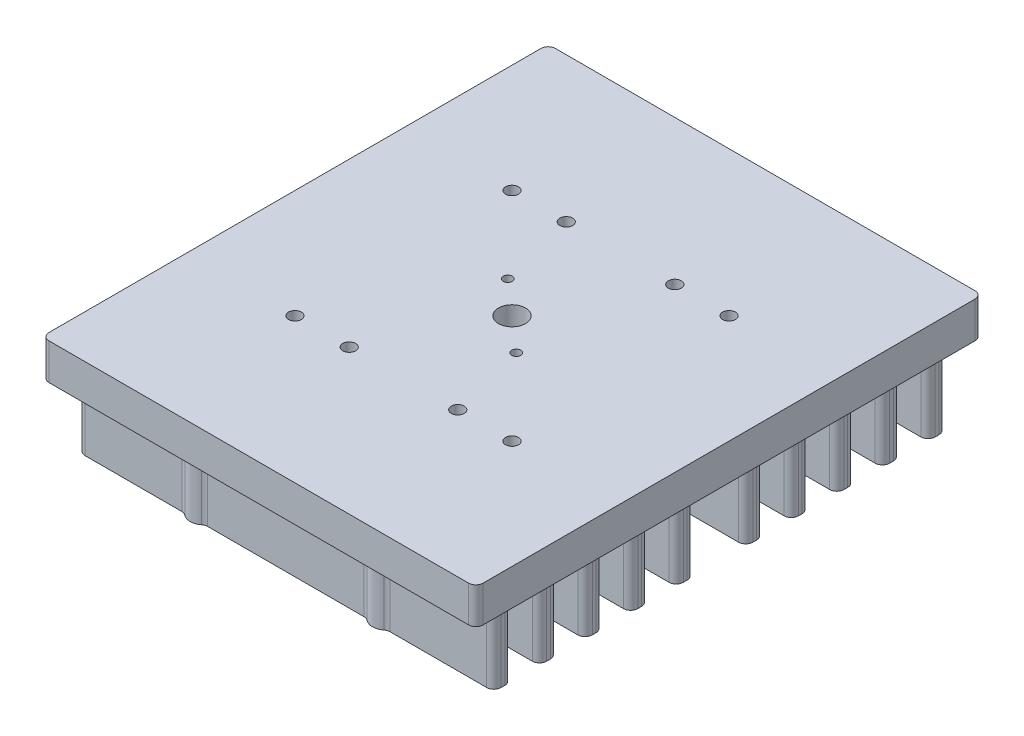
SolidWorks part; units mm, degrees
material "6061-T6 (SS)"
ref_plane "Front Plane" through (0, 0, 0) normal (0, 0, 1) x (1, 0, 0)
ref_plane "Top Plane" through (0, 0, 0) normal (0, 1, 0) x (1, 0, 0)
ref_plane "Right Plane" through (0, 0, 0) normal (1, 0, 0) x (0, 0, -1)
sketch "Sketch1" plane through (0, 0, 0) normal (0, 1, 0) x (1, 0, 0)
  line L1 (25.4, -25.4) -> (-25.4, -25.4) construction
  line L2 (25.4, -25.4) -> (25.4, 25.4) construction
  line L3 (25.4, 25.4) -> (-25.4, 25.4) construction
  line L4 (-25.4, -25.4) -> (-25.4, 25.4) construction
  line L5 (25.4, -25.4) -> (-25.4, 25.4) construction
  line L6 (25.4, 25.4) -> (-25.4, -25.4) construction
  line L7 (-38.1, 44.45) -> (38.1, 44.45)
  line L8 (-38.1, 44.45) -> (-38.1, -44.45)
  line L9 (-38.1, -44.45) -> (38.1, -44.45)
  line L10 (38.1, 44.45) -> (38.1, -44.45)
  line L11 (-38.1, 44.45) -> (38.1, -44.45) construction
  line L12 (-38.1, -44.45) -> (38.1, 44.45) construction
  point P0 (0, 0)
  point P6 (0, 0)
  dimension "D1" = 50.8
  dimension "D2" = 50.8
  dimension "D3" = 76.2
  dimension "D4" = 88.9
extrude "Boss-Extrude1" add sketch "Sketch1" along normal blind 6.35
hole_wizard "#4-40 Tapped Hole1" positions "Sketch2" profile "Sketch3" tap size "#4-40" standard "ANSI Inch" end condition through all
sketch "Sketch2" plane through (0, 6.35, 0) normal (0, 1, 0) x (1, 0, 0)
  line L1 (-19.05, 19.05) -> (19.05, 19.05)
  line L2 (-19.05, 19.05) -> (-19.05, -19.05)
  line L3 (-19.05, -19.05) -> (19.05, -19.05)
  line L4 (19.05, 19.05) -> (19.05, -19.05)
  line L5 (-19.05, 19.05) -> (19.05, -19.05) construction
  line L6 (-19.05, -19.05) -> (19.05, 19.05) construction
  point P2 (19.05, -19.05)
  point P51 (-19.05, 19.05)
  point P52 (-19.05, -19.05)
  point P53 (19.05, 19.05)
  dimension "D1" = 38.1
  dimension "D2" = 38.1
sketch "Sketch3" plane through (19.05, 6.35, 19.05) normal (1, 0, 0) x (0, 0, 1)
  line L0 (0, 0) -> (0, 6.35)
  line L1 (0, 6.35) -> (1.1303, 6.35)
  line L2 (1.1303, 6.35) -> (1.1303, 0)
  line L5 (1.1303, 0) -> (0, 0)
  line L11 (0, -6.35) -> (0, 107.95) construction
  dimension "Thru Tap Drill Dia." = 2.2606
  dimension "Thru Tap Drill Depth" = 6.35
cosmetic thread "Hole Thread1" parameters "D2"=2.8448
cosmetic thread "Hole Thread2" parameters "D2"=2.8448
cosmetic thread "Hole Thread3" parameters "D2"=2.8448
cosmetic thread "Hole Thread4" parameters "D2"=2.8448
hole_wizard "M2x0.4 Tapped Hole1" positions "Sketch4" profile "Sketch5" tap size "M2x0.4" standard "ANSI Metric" end condition through all
sketch "Sketch4" plane through (0, 6.35, 0) normal (0, 1, 0) x (1, 0, 0)
  line L0 (-6, 5.25) -> (6, -5.25) construction
  point P0 (-6, 5.25)
  point P2 (6, -5.25)
  dimension "D1" = 12
  dimension "D2" = 10.5
sketch "Sketch5" plane through (-6, 6.35, -5.25) normal (1, 0, 0) x (0, 0, 1)
  line L0 (0, 0) -> (0, 6.35)
  line L1 (0, 6.35) -> (0.8, 6.35)
  line L2 (0.8, 6.35) -> (0.8, 0)
  line L5 (0.8, 0) -> (0, 0)
  line L11 (0, -6.35) -> (0, 107.95) construction
  dimension "Thru Tap Drill Dia." = 1.6
  dimension "Thru Tap Drill Depth" = 6.35
cosmetic thread "Hole Thread5" parameters "D2"=2
cosmetic thread "Hole Thread6" parameters "D2"=2
sketch "Sketch6" plane through (0, 0, 0) normal (0, -1, 0) x (1, 0, 0)
  line L0 (0, 22.1) -> (0, 0) construction
  line L1 (-16, 38.1) -> (16, 38.1) construction
  line L2 (-16, 38.1) -> (-16, 6.1) construction
  line L3 (-16, 6.1) -> (16, 6.1) construction
  line L4 (16, 38.1) -> (16, 6.1) construction
  line L5 (-16, 38.1) -> (16, 6.1) construction
  line L6 (-16, 6.1) -> (16, 38.1) construction
  line L8 (-38.1, 44.45) -> (38.1, 44.45) construction
  line L9 (-1000, 0) -> (49000, 0) construction
  line L10 (-16, -6.1) -> (16, -38.1) construction
  line L11 (-16, -38.1) -> (16, -6.1) construction
  line L12 (16, -38.1) -> (16, -6.1) construction
  line L13 (-16, -6.1) -> (16, -6.1) construction
  line L14 (-16, -38.1) -> (-16, -6.1) construction
  line L15 (-16, -38.1) -> (16, -38.1) construction
  circle A0 centre (-16, 38.1) radius 2.3812
  circle A1 centre (16, 38.1) radius 2.3813
  arc A2 (18.3813, 6.1) -> (13.6188, 6.1) centre (16, 6.1) ccw construction
  arc A3 (-13.6187, 6.1) -> (-18.3813, 6.1) centre (-16, 6.1) ccw construction
  circle A4 centre (-16, 6.1) radius 2.3813
  circle A5 centre (16, 6.1) radius 2.3812
  arc A6 (-13.6187, -6.1) -> (-18.3813, -6.1) centre (-16, -6.1) cw construction
  arc A7 (18.3813, -6.1) -> (13.6188, -6.1) centre (16, -6.1) cw construction
  circle A8 centre (16, -6.1) radius 2.3812
  circle A9 centre (-16, -6.1) radius 2.3813
  circle A10 centre (16, -38.1) radius 2.3813
  circle A11 centre (-16, -38.1) radius 2.3812
  point P0 (0, 0)
  dimension "D3" = 4.7625
  dimension "D1" = 32
  dimension "D2" = 32
  dimension "D4" = 6.35
extrude "Boss-Extrude2" add sketch "Sketch6" along normal blind 12.7
sketch "Sketch9" plane through (0, 0, 0) normal (0, -1, 0) x (1, 0, 0)
  line L0 (-36.5125, 38.1) -> (-16, 38.1) construction
  line L1 (-36.5125, 39.6875) -> (36.5125, 39.6875)
  line L2 (-36.5125, 39.6875) -> (-36.5125, 36.5125)
  line L3 (-36.5125, 36.5125) -> (36.5125, 36.5125)
  line L4 (36.5125, 39.6875) -> (36.5125, 36.5125)
  line L5 (-38.1, -44.45) -> (-38.1, 44.45) construction
  line L6 (-36.5125, 31.6875) -> (36.5125, 31.6875)
  line L7 (-36.5125, 31.6875) -> (-36.5125, 28.5125)
  line L8 (-36.5125, 28.5125) -> (36.5125, 28.5125)
  line L9 (36.5125, 31.6875) -> (36.5125, 28.5125)
  line L10 (-36.5125, 23.6875) -> (36.5125, 23.6875)
  line L11 (-36.5125, 23.6875) -> (-36.5125, 20.5125)
  line L12 (-36.5125, 20.5125) -> (36.5125, 20.5125)
  line L13 (36.5125, 23.6875) -> (36.5125, 20.5125)
  line L14 (-36.5125, 15.6875) -> (36.5125, 15.6875)
  line L15 (-36.5125, 15.6875) -> (-36.5125, 12.5125)
  line L16 (-36.5125, 12.5125) -> (36.5125, 12.5125)
  line L17 (36.5125, 15.6875) -> (36.5125, 12.5125)
  line L18 (38.1, 44.45) -> (38.1, -44.45) construction
  line L19 (-38.1, 44.45) -> (38.1, 44.45) construction
  line L20 (-36.5125, 36.5125) -> (-36.5125, 31.6875) construction
  line L21 (-36.5125, 28.5125) -> (-36.5125, 23.6875) construction
  line L22 (-36.5125, 20.5125) -> (-36.5125, 15.6875) construction
  line L23 (-36.5125, 12.5125) -> (-36.5125, 7.6875) construction
  line L24 (-36.5125, -6.1) -> (-16, -6.1) construction
  line L25 (-36.5125, 7.6875) -> (36.5125, 7.6875)
  line L26 (-36.5125, 7.6875) -> (-36.5125, 4.5125)
  line L27 (-36.5125, -12.5125) -> (-36.5125, -7.6875) construction
  line L28 (-36.5125, 6.1) -> (-16, 6.1) construction
  line L29 (-1000, 0) -> (49000, 0) construction
  line L30 (-36.5125, -20.5125) -> (-36.5125, -15.6875) construction
  line L31 (-36.5125, -28.5125) -> (-36.5125, -23.6875) construction
  line L32 (-36.5125, -36.5125) -> (-36.5125, -31.6875) construction
  line L33 (-36.5125, -38.1) -> (-16, -38.1) construction
  line L34 (-36.5125, 4.5125) -> (36.5125, 4.5125)
  line L35 (36.5125, 7.6875) -> (36.5125, 4.5125)
  line L36 (36.5125, -7.6875) -> (36.5125, -4.5125)
  line L37 (-36.5125, -4.5125) -> (36.5125, -4.5125)
  line L38 (-36.5125, -7.6875) -> (-36.5125, -4.5125)
  line L39 (-36.5125, -7.6875) -> (36.5125, -7.6875)
  line L40 (36.5125, -15.6875) -> (36.5125, -12.5125)
  line L41 (-36.5125, -12.5125) -> (36.5125, -12.5125)
  line L42 (-36.5125, -15.6875) -> (-36.5125, -12.5125)
  line L43 (-36.5125, -15.6875) -> (36.5125, -15.6875)
  line L44 (36.5125, -23.6875) -> (36.5125, -20.5125)
  line L45 (-36.5125, -20.5125) -> (36.5125, -20.5125)
  line L46 (-36.5125, -23.6875) -> (-36.5125, -20.5125)
  line L47 (-36.5125, -23.6875) -> (36.5125, -23.6875)
  line L48 (36.5125, -31.6875) -> (36.5125, -28.5125)
  line L49 (-36.5125, -28.5125) -> (36.5125, -28.5125)
  line L50 (-36.5125, -31.6875) -> (-36.5125, -28.5125)
  line L51 (-36.5125, -31.6875) -> (36.5125, -31.6875)
  line L52 (36.5125, -39.6875) -> (36.5125, -36.5125)
  line L53 (-36.5125, -36.5125) -> (36.5125, -36.5125)
  line L54 (-36.5125, -39.6875) -> (-36.5125, -36.5125)
  line L55 (-36.5125, -39.6875) -> (36.5125, -39.6875)
  dimension "D1" = 1.5875
  dimension "D2" = 1.5875
  dimension "D3" = 4.7625
  dimension "D4" = 4.825
extrude "Boss-Extrude3" add sketch "Sketch9" along normal blind 12.7
hole_wizard "#6-32 Tapped Hole1" positions "Sketch7" profile "Sketch8" tap size "#6-32" standard "ANSI Inch"
sketch "Sketch7" plane through (0, -12.7, 0) normal (0, -1, 0) x (-1, 0, 0)
  point P0 (16, -38.1)
  point P3 (-16, -38.1)
  point P32 (-16, 38.1)
  point P35 (16, 38.1)
  point P38 (-16, 6.1)
  point P41 (16, 6.1)
  point P43 (16, -6.1)
  point P46 (-16, -6.1)
cosmetic thread "Hole Thread7" [suppressed] parameters "D1"=7.0104, "D2"=3.5052
cosmetic thread "Hole Thread8" [suppressed] parameters "D1"=7.0104, "D2"=3.5052
cosmetic thread "Hole Thread9" [suppressed] parameters "D1"=7.0104, "D2"=3.5052
cosmetic thread "Hole Thread10" [suppressed] parameters "D1"=7.0104, "D2"=3.5052
sketch "Sketch8" plane through (-16, -12.7, 38.1) normal (1, 0, 0) x (0, 0, -1)
  line L0 (0, 0) -> (0, 10.2107)
  line L1 (0, 10.2107) -> (1.3525, 9.398)
  line L2 (1.3525, 9.398) -> (1.3525, 0)
  line L5 (1.3525, 0) -> (0, 0)
  line L10 (0, 10.2107) -> (-1.3525, 9.398) construction
  line L11 (0, -6.35) -> (0, 107.95) construction
  dimension "Tap Drill Dia." = 2.7051
  dimension "Tap Drill Depth" = 9.398
  dimension "Drill Angle" = 118
cosmetic thread "Hole Thread11" parameters "D1"=7.0104, "D2"=3.5052
cosmetic thread "Hole Thread12" parameters "D1"=7.0104, "D2"=3.5052
cosmetic thread "Hole Thread13" parameters "D1"=7.0104, "D2"=3.5052
cosmetic thread "Hole Thread14" parameters "D1"=7.0104, "D2"=3.5052
fillet "Fillet1" radius 1.27 76 edges at (-17.7749, -6.35, 39.6875) (-14.2251, -6.35, 39.6875) (14.2251, -6.35, 39.6875) (17.7749, -6.35, 39.6875) (-14.2251, -6.35, 36.5125) (-17.7749, -6.35, 36.5125) (17.7749, -6.35, 36.5125) (14.2251, -6.35, 36.5125) (36.5125, -6.35, 39.6875) (36.5125, -6.35, 36.5125) (36.5125, -6.35, 31.6875) (36.5125, -6.35, 28.5125) (36.5125, -6.35, 23.6875) (36.5125, -6.35, 20.5125) (36.5125, -6.35, 15.6875) (36.5125, -6.35, 12.5125) (-36.5125, -6.35, 39.6875) (-36.5125, -6.35, 36.5125) (-36.5125, -6.35, 31.6875) (-36.5125, -6.35, 28.5125) (-36.5125, -6.35, 23.6875) (-36.5125, -6.35, 20.5125) (-36.5125, -6.35, 15.6875) (-36.5125, -6.35, 12.5125) (-36.5125, -6.35, -39.6875) (-36.5125, -6.35, -36.5125) (-36.5125, -6.35, -31.6875) (-36.5125, -6.35, -28.5125) (-36.5125, -6.35, -23.6875) (-36.5125, -6.35, -20.5125) (-36.5125, -6.35, -15.6875) (-36.5125, -6.35, -12.5125) (-36.5125, -6.35, -7.6875) (-36.5125, -6.35, -4.5125) (-36.5125, -6.35, 4.5125) (-36.5125, -6.35, 7.6875) (14.2251, -6.35, -36.5125) (17.7749, -6.35, -36.5125) (-17.7749, -6.35, -36.5125) (-14.2251, -6.35, -36.5125) (17.7749, -6.35, -39.6875) (14.2251, -6.35, -39.6875) (-14.2251, -6.35, -39.6875) (-17.7749, -6.35, -39.6875) (17.7749, -6.35, -7.6875) (14.2251, -6.35, -7.6875) (-14.2251, -6.35, -7.6875) (-17.7749, -6.35, -7.6875) (14.2251, -6.35, -4.5125) (17.7749, -6.35, -4.5125) (-17.7749, -6.35, -4.5125) (-14.2251, -6.35, -4.5125) (17.7749, -6.35, 4.5125) (14.2251, -6.35, 4.5125) (-14.2251, -6.35, 4.5125) (-17.7749, -6.35, 4.5125) (-17.7749, -6.35, 7.6875) (-14.2251, -6.35, 7.6875) (14.2251, -6.35, 7.6875) (17.7749, -6.35, 7.6875) (36.5125, -6.35, -39.6875) (36.5125, -6.35, -36.5125) (36.5125, -6.35, -31.6875) (36.5125, -6.35, -28.5125) (36.5125, -6.35, -23.6875) (36.5125, -6.35, -20.5125) (36.5125, -6.35, -15.6875) (36.5125, -6.35, -12.5125) (36.5125, -6.35, -7.6875) (36.5125, -6.35, -4.5125) (36.5125, -6.35, 7.6875) (36.5125, -6.35, 4.5125) (38.1, 3.175, -44.45) (-38.1, 3.175, -44.45) (38.1, 3.175, 44.45) (-38.1, 3.175, 44.45)
sketch "Sketch10" plane through (0, 6.35, 0) normal (0, 1, 0) x (1, 0, 0)
  circle A0 centre (0, 0) radius 2.3813
  dimension "D1" = 4.7625
extrude "Cut-Extrude1" cut sketch "Sketch10" against normal through all
hole_wizard "#4-40 Tapped Hole2" positions "Sketch11" profile "Sketch12" tap size "#4-40" standard "ANSI Inch"
sketch "Sketch11" plane through (-33.5042, 6.35, -53.7367) normal (0, 1, 0) x (1, 0, 0)
  point P0 (43.0292, -34.6867)
  point P3 (23.9792, -34.6867)
  point P6 (23.9792, -72.7867)
  point P9 (43.0292, -72.7867)
sketch "Sketch12" plane through (9.525, 6.35, -19.05) normal (1, 0, 0) x (0, 0, 1)
  line L0 (0, 0) -> (0, 9.4422)
  line L1 (0, 9.4422) -> (1.1303, 8.763)
  line L2 (1.1303, 8.763) -> (1.1303, 0)
  line L3 (1.1303, 0) -> (0, 0)
  line L4 (0, 9.4422) -> (-1.1303, 8.763) construction
  line L5 (0, -6.35) -> (0, 107.95) construction
  dimension "Tap Drill Dia." = 2.2606
  dimension "Tap Drill Depth" = 8.763
  dimension "Drill Angle" = 118
cosmetic thread "Hole Thread15"
cosmetic thread "Hole Thread16"
cosmetic thread "Hole Thread17"
cosmetic thread "Hole Thread18"
